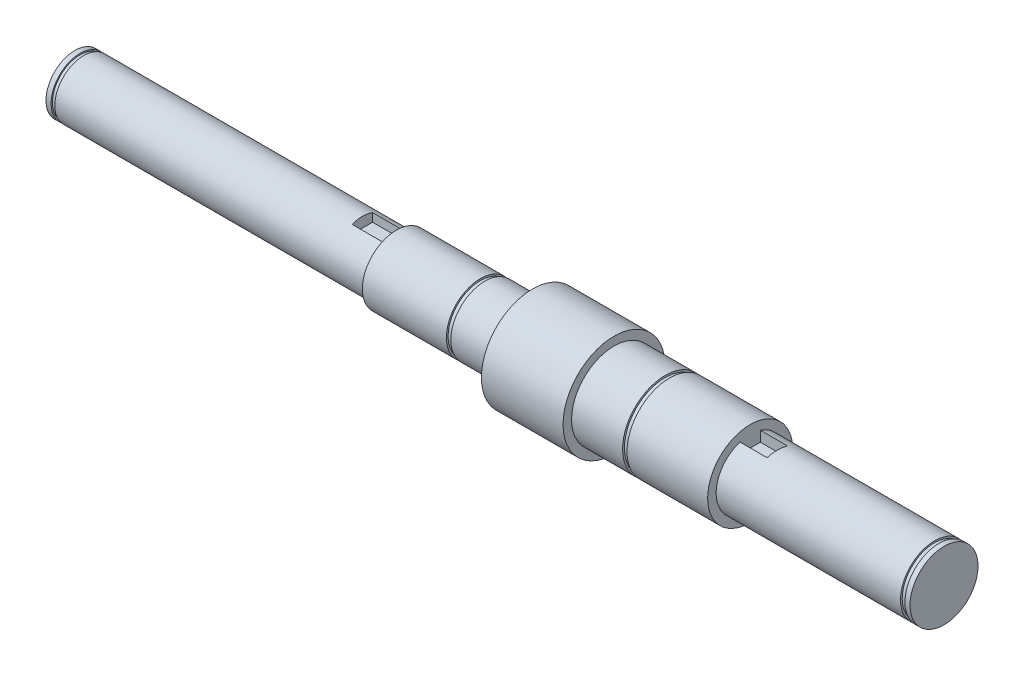
SolidWorks part; units mm, degrees
ref_plane "Front Plane" through (0, 0, 0) normal (0, 0, 1) x (1, 0, 0)
ref_plane "Top Plane" through (0, 0, 0) normal (0, 1, 0) x (1, 0, 0)
ref_plane "Right Plane" through (0, 0, 0) normal (1, 0, 0) x (0, 0, -1)
sketch "Sketch1" plane through (0, 0, 0) normal (0, 0, 1) x (1, 0, 0)
  line L0 (-127.75, 0) -> (127.75, 0)
  line L1 (-127.75, 0) -> (-127.75, 8.5)
  line L2 (-127.75, 8.5) -> (-126.25, 8.5)
  line L3 (-33.25, 8.5) -> (-33.25, 10)
  line L4 (-33.25, 10) -> (-8.55, 10)
  line L5 (6.75, 10) -> (6.75, 15)
  line L6 (6.75, 15) -> (30.75, 15)
  line L7 (30.75, 15) -> (30.75, 12.5)
  line L8 (30.75, 12.5) -> (45.75, 12.5)
  line L9 (70.75, 12.5) -> (70.75, 10)
  line L10 (70.75, 10) -> (124.95, 10)
  line L11 (127.75, 10) -> (127.75, 0)
  line L12 (-125.15, 8.5) -> (-33.25, 8.5)
  line L14 (-126.25, 8.5) -> (-126.25, 8.1)
  line L15 (-126.25, 8.1) -> (-125.15, 8.1)
  line L16 (-125.15, 8.5) -> (-125.15, 8.1)
  line L17 (126.25, 10) -> (127.75, 10)
  line L19 (124.95, 10) -> (124.95, 9.5)
  line L20 (124.95, 9.5) -> (126.25, 9.5)
  line L21 (126.25, 10) -> (126.25, 9.5)
  line L22 (-7.25, 10) -> (6.75, 10)
  line L24 (-8.55, 10) -> (-8.55, 9.5)
  line L25 (-8.55, 9.5) -> (-7.25, 9.5)
  line L26 (-7.25, 10) -> (-7.25, 9.5)
  line L27 (47.05, 12.5) -> (70.75, 12.5)
  line L29 (45.75, 12.5) -> (45.75, 11.95)
  line L30 (45.75, 11.95) -> (47.05, 11.95)
  line L31 (47.05, 12.5) -> (47.05, 11.95)
  point P4 (0, 0)
  point P19 (-125.15, 8.3)
  point P31 (46.0186, 11.95)
  dimension "D1" = 255.5
  dimension "D2" = 8.5
  dimension "D3" = 94.5
  dimension "D4" = 40
  dimension "D5" = 24
  dimension "D6" = 40
  dimension "D7" = 57
  dimension "D8" = 10
  dimension "D9" = 15
  dimension "D10" = 12.5
  dimension "D11" = 10
  dimension "D12" = 1.5
  dimension "D13" = 0.4
  dimension "D14" = 1.1
  dimension "D15" = 1.3
  dimension "D16" = 0.5
  dimension "D17" = 1.5
  dimension "D18" = 14
  dimension "D19" = 1.3
  dimension "D20" = 0.5
  dimension "D21" = 1.3
  dimension "D22" = 0.55
  dimension "D23" = 15
revolve "Revolve1" add sketch "Sketch1" angle 360 about L0
sketch "Sketch2" plane through (-33.25, 0, 0) normal (-1, 0, 0) x (0, 0, 1)
  line L0 (0, 8.5) -> (0, 0) construction
  line L1 (-3, 5.5) -> (3, 5.5)
  line L2 (-3, 5.5) -> (-3, 10.8)
  line L3 (-3, 10.8) -> (3, 10.8)
  line L4 (3, 5.5) -> (3, 10.8)
  circle A0 centre (0, 0) radius 8.5 construction
  circle A1 centre (0, 0) radius 8.5 construction
  point P11 (-2.1633, 9.108)
  point P12 (-2.0398, 11.0493)
  dimension "D1" = 3
  dimension "D2" = 2.3
  dimension "D3" = 6
extrude "Cut-Extrude1" cut sketch "Sketch2" along normal blind 10
sketch "Sketch3" plane through (70.75, 0, 0) normal (1, 0, 0) x (0, 0, -1)
  line L0 (0, 10) -> (0, 0) construction
  line L1 (-3, 10) -> (3, 10)
  line L2 (-3, 10) -> (-3, 6.5)
  line L3 (-3, 6.5) -> (3, 6.5)
  line L4 (3, 10) -> (3, 6.5)
  circle A0 centre (0, 0) radius 10 construction
  circle A1 centre (0, 0) radius 10 construction
  dimension "D1" = 3.5
  dimension "D2" = 6
extrude "Cut-Extrude2" cut sketch "Sketch3" along normal blind 8
